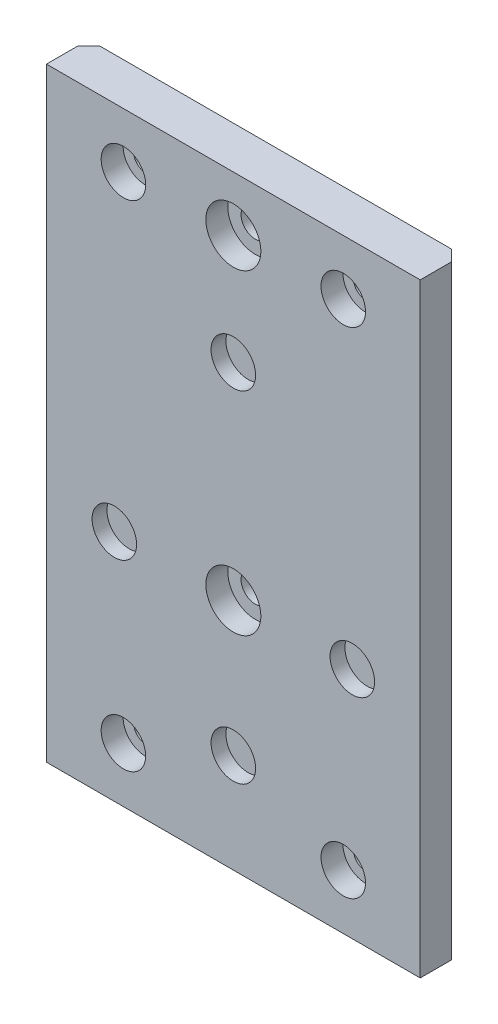
SolidWorks part; units mm, degrees
ref_plane "Front Plane" through (0, 0, 0) normal (0, 0, 1) x (1, 0, 0)
ref_plane "Top Plane" through (0, 0, 0) normal (0, 1, 0) x (1, 0, 0)
ref_plane "Right Plane" through (0, 0, 0) normal (1, 0, 0) x (0, 0, -1)
sketch "Sketch1" plane through (0, 0, 0) normal (0, 0, 1) x (1, 0, 0)
  line L0 (0, -45) -> (0, -41) construction
  line L1 (-34, 55) -> (34, 55)
  line L2 (-34, 55) -> (-34, -55)
  line L3 (-34, -55) -> (34, -55)
  line L4 (34, 55) -> (34, -55)
  line L5 (-34, 55) -> (34, -55) construction
  line L6 (-34, -55) -> (34, 55) construction
  line L7 (-20, 45) -> (20, 45) construction
  line L8 (-20, 45) -> (-20, -45) construction
  line L9 (-20, -45) -> (20, -45) construction
  line L10 (20, 45) -> (20, -45) construction
  line L11 (-20, 45) -> (20, -45) construction
  line L12 (-20, -45) -> (20, 45) construction
  line L13 (0, 25) -> (-21.6506, -12.5) construction
  line L14 (-21.6506, -12.5) -> (21.6506, -12.5) construction
  line L15 (21.6506, -12.5) -> (0, 25) construction
  circle A0 centre (20, 45) radius 2.1
  circle A1 centre (-20, 45) radius 2.1
  circle A2 centre (20, -45) radius 2.1
  circle A3 centre (-20, -45) radius 2.1
  circle A4 centre (0, 0) radius 25 construction
  circle A5 centre (21.6506, -12.5) radius 4.05
  circle A6 centre (0, 25) radius 4.05
  circle A7 centre (-21.6506, -12.5) radius 4.05
  circle A9 centre (0, -36.95) radius 4.05
  circle A10 centre (0, 45) radius 2.6
  circle A11 centre (0, -12.5) radius 2.6
  point P0 (0, 0)
  point P6 (0, 0)
extrude "Boss-Extrude1" add sketch "Sketch1" along normal blind 7.7
sketch "Sketch2" plane through (0, 0, 0) normal (0, 0, -1) x (-1, 0, 0)
  circle A0 centre (-21.6506, -12.5) radius 6.3046
  circle A1 centre (0, 25) radius 7.3343
  circle A2 centre (21.6506, -12.5) radius 8.114
  circle A3 centre (0, -36.95) radius 11.0737
extrude "Boss-Extrude2" add sketch "Sketch2" against normal blind 5
sketch "Sketch3" plane through (0, 0, 7.7) normal (0, 0, -1) x (-1, 0, 0)
  circle A0 centre (-20, 45) radius 4.05
  circle A1 centre (20, 45) radius 4.05
  circle A2 centre (-20, -45) radius 4.05
  circle A3 centre (20, -45) radius 4.05
  circle A4 centre (0, 45) radius 5
  circle A5 centre (0, -12.5) radius 5
extrude "Cut-Extrude1" cut sketch "Sketch3" along normal blind 4
sketch "Sketch4" plane through (0, -55, 0) normal (0, -1, 0) x (1, 0, 0)
  line L0 (0, 0) -> (0, 14.6488) construction
  line L1 (-34, 0) -> (34, 0) construction
  line L2 (-34, 0) -> (-26.07, -6.4369) construction
  line L3 (-34, 7.7) -> (-37.4959, 19.6552) construction
  line L10 (0.55, -7.7) -> (0.55, 5.4137) construction
  line L22 (-34, 7.7) -> (34, 7.7) construction
  line L26 (4.3768, 7.7) -> (4.3768, 0) construction
  line L27 (4.3768, 0) -> (4.3768, 3.85) construction
  line L28 (4.3768, 3.85) -> (9.9473, 3.85) construction
  line L29 (34, 2) -> (34, 0)
  line L30 (32, 0) -> (34, 2)
  line L31 (34, 0) -> (32, 0)
  line L32 (-34, 15.4) -> (-39, 15.4)
  line L33 (-34, 2) -> (-34, 15.4)
  line L34 (-32, 0) -> (-34, 2)
  line L35 (-39, 0) -> (-39, 15.4)
  line L36 (-34, 0) -> (-39, 0)
  line L37 (-34, 0) -> (-32, 0)
extrude "Cut-Extrude2" cut sketch "Sketch4" against normal through all
